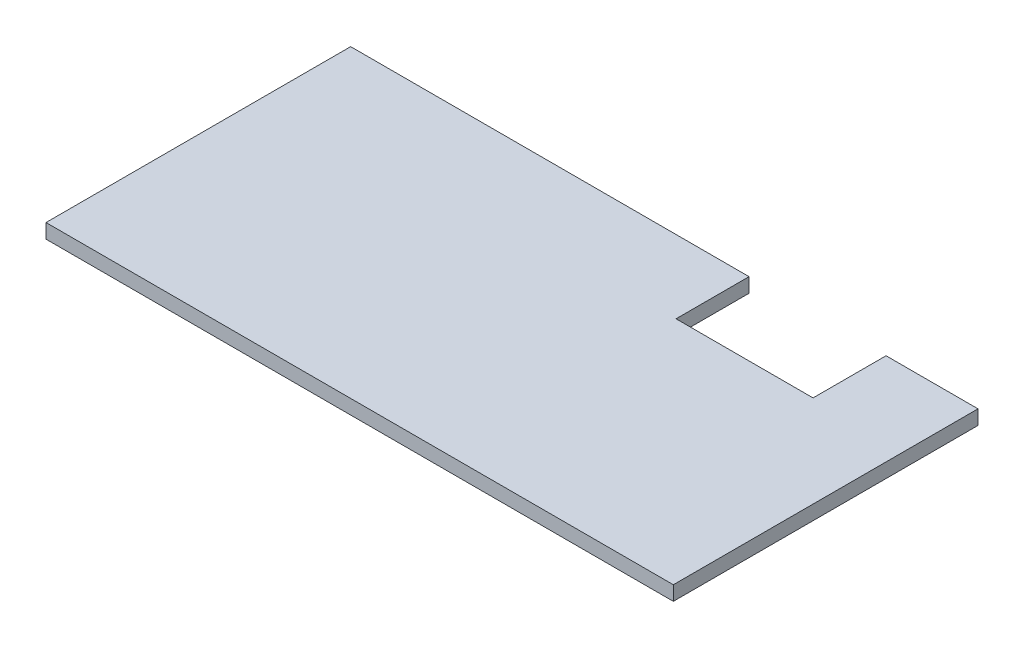
SolidWorks part; units mm, degrees
material "E-Glass Fiber"
ref_plane "Front Plane" through (0, 0, 0) normal (0, 0, 1) x (1, 0, 0)
ref_plane "Top Plane" through (0, 0, 0) normal (0, 1, 0) x (1, 0, 0)
ref_plane "Right Plane" through (0, 0, 0) normal (1, 0, 0) x (0, 0, -1)
sketch "Sketch1" plane through (0, 0, 0) normal (0, 1, 0) x (1, 0, 0)
  line L0 (0, 7.62) -> (-29.8, 7.62) construction
  line L1 (-29.8, 24.52) -> (39.8, 24.52)
  line L2 (-29.8, 24.52) -> (-29.8, -9.28)
  line L3 (-29.8, -9.28) -> (39.8, -9.28)
  line L4 (39.8, 24.52) -> (39.8, -9.28)
  line L5 (0, 0) -> (10, 0) construction
  line L6 (0, 0) -> (0, 15.24) construction
  line L7 (0, 15.24) -> (10, 15.24) construction
  line L8 (10, 0) -> (10, 15.24) construction
  line L10 (10, 7.62) -> (39.8, 7.62) construction
  dimension "D1" = 69.6
  dimension "D2" = 33.8
  dimension "D3" = 15.24
  dimension "D4" = 10
extrude "Boss-Extrude2" add sketch "Sketch1" along normal blind 1.6
sketch "Sketch2" plane through (0, 0, 0) normal (0, 1, 0) x (1, 0, 0)
  line L0 (0, -0.88) -> (0, 0.88) construction
  line L2 (-0.88, 0) -> (0.88, 0) construction
  circle A0 centre (0, 0) radius 0.45
  circle A1 centre (0, 15.24) radius 0.45
  dimension "D1" = 0.9
  dimension "D2" = 15.24
extrude "Cut-Extrude2" [suppressed] cut sketch "Sketch2" along normal blind 1.6
sketch "Sketch3" plane through (0, 0, 0) normal (0, 1, 0) x (1, 0, 0)
  line L1 (-0.88, 0) -> (0.88, 0) construction
  line L2 (0, -0.88) -> (0, 0.88) construction
  circle A0 centre (-0.127, 10.16) radius 0.5
  circle A1 centre (2.413, 10.16) radius 0.5
  circle A2 centre (2.413, 7.62) radius 0.5
  circle A3 centre (2.413, 5.08) radius 0.5
  circle A4 centre (-0.127, 5.08) radius 0.5
  circle A5 centre (-0.127, 7.62) radius 0.5
  dimension "D1" = 1
  dimension "D5" = 7.62
  dimension "D2" = 2.54
  dimension "D3" = 2.54
  dimension "D4" = 2.54
  dimension "D7" = 0.127
extrude "Cut-Extrude4" [suppressed] cut sketch "Sketch3" along normal blind 1.6
ref_plane "Plane3" through (0, 0, -5.08) normal (0, 0, 1) x (1, 0, 0)
other "Move Face1" [suppressed] parameters "D1"=2.54
other "Move Face2" [suppressed] parameters "D1"=14
sketch "Sketch4" plane through (0, 0, 0) normal (0, 1, 0) x (1, 0, 0)
  line L0 (-0.88, 0) -> (0.88, 0) construction
  line L1 (0, -0.88) -> (0, 0.88) construction
  line L2 (39.8, -9.28) -> (39.8, 24.52) construction
  circle A0 centre (37.78, 15.24) radius 0.9
  circle A1 centre (37.78, 0) radius 0.9
  circle A2 centre (2.54, 0) radius 0.9
  circle A3 centre (2.54, 15.24) radius 0.9
  dimension "D3" = 1.8
  dimension "D1" = 2.02
  dimension "D2" = 2.54
  dimension "D4" = 15.24
  dimension "D5" = 15.24
extrude "Cut-Extrude5" [suppressed] cut sketch "Sketch4" along normal blind 1.6
sketch "Sketch5" plane through (0, 1.6, 0) normal (0, 1, 0) x (1, 0, 0)
  line L0 (39.8, 24.52) -> (-29.8, 24.52) construction
  line L1 (29.6, 24.52) -> (14.4, 24.52)
  line L2 (29.6, 24.52) -> (29.6, 16.42)
  line L3 (29.6, 16.42) -> (14.4, 16.42)
  line L4 (14.4, 24.52) -> (14.4, 16.42)
  line L5 (39.8, -9.28) -> (39.8, 24.52) construction
  dimension "D1" = 10.2
  dimension "D2" = 15.2
  dimension "D3" = 8.1
extrude "Cut-Extrude6" cut sketch "Sketch5" against normal blind 10
